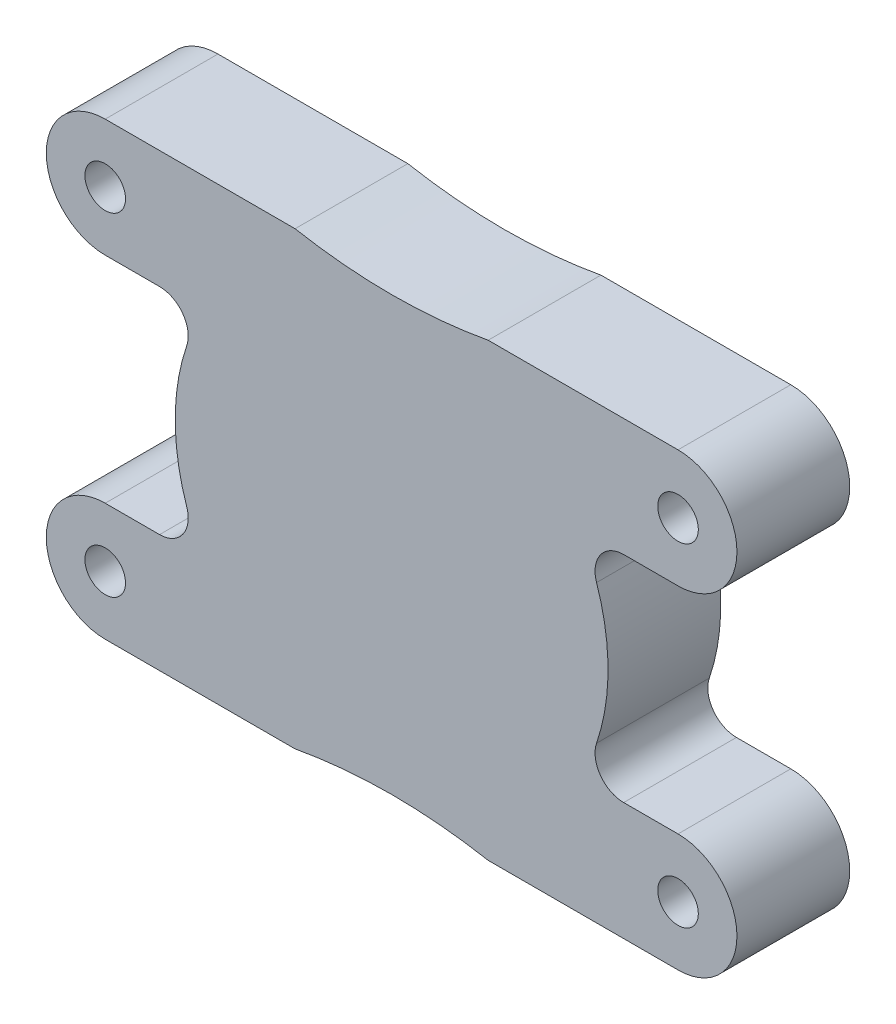
SolidWorks part; units mm, degrees
ref_plane "Front Plane" through (0, 0, 0) normal (0, 0, 1) x (1, 0, 0)
ref_plane "Top Plane" through (0, 0, 0) normal (0, 1, 0) x (1, 0, 0)
ref_plane "Right Plane" through (0, 0, 0) normal (1, 0, 0) x (0, 0, -1)
sketch "Sketch1" plane through (0, 0, 0) normal (0, 0, 1) x (1, 0, 0)
  line L8 (8.5626, -19.975) -> (25.4, -19.975)
  line L9 (25.4, -9.525) -> (20.5798, -9.525)
  line L10 (20.5798, 9.525) -> (25.4, 9.525)
  line L11 (25.4, 19.975) -> (8.5626, 19.975)
  line L12 (-8.5626, 19.975) -> (-25.4, 19.975)
  line L13 (-25.4, 9.525) -> (-20.5798, 9.525)
  line L14 (-20.5798, -9.525) -> (-25.4, -9.525)
  line L15 (-25.4, -19.975) -> (-8.5626, -19.975)
  line L16 (8.5626, -19.975) -> (25.4, -19.975)
  line L17 (25.4, -9.525) -> (20.5798, -9.525)
  line L18 (20.5798, 9.525) -> (25.4, 9.525)
  line L19 (25.4, 19.975) -> (8.5626, 19.975)
  line L20 (-8.5626, 19.975) -> (-25.4, 19.975)
  line L21 (-25.4, 9.525) -> (-20.5798, 9.525)
  line L22 (-20.5798, -9.525) -> (-25.4, -9.525)
  line L23 (-25.4, -19.975) -> (-8.5626, -19.975)
  circle A0 centre (-25.4, -14.75) radius 1.8 construction
  circle A1 centre (-25.4, 14.75) radius 1.8 construction
  circle A2 centre (25.4, -14.75) radius 1.8 construction
  circle A3 centre (25.4, 14.75) radius 1.8 construction
  circle A4 centre (-25.4, 14.75) radius 1.8
  circle A5 centre (-25.4, -14.75) radius 1.8
  circle A6 centre (25.4, -14.75) radius 1.8
  circle A7 centre (25.4, 14.75) radius 1.8
  arc A12 (8.5626, -19.975) -> (-8.5626, -19.975) centre (0, -66.4554) ccw
  arc A13 (25.4, -19.975) -> (25.4, -9.525) centre (25.4, -14.75) ccw
  arc A14 (18.1746, -6.1686) -> (20.5798, -9.525) centre (20.5798, -6.985) ccw
  arc A15 (18.1746, -6.1686) -> (18.1746, 6.1686) centre (0, 0) ccw
  arc A16 (20.5798, 9.525) -> (18.1746, 6.1686) centre (20.5798, 6.985) ccw
  arc A17 (25.4, 9.525) -> (25.4, 19.975) centre (25.4, 14.75) ccw
  arc A18 (-8.5626, 19.975) -> (8.5626, 19.975) centre (0, 66.4554) ccw
  arc A19 (-25.4, 19.975) -> (-25.4, 9.525) centre (-25.4, 14.75) ccw
  arc A20 (-18.1746, 6.1686) -> (-20.5798, 9.525) centre (-20.5798, 6.985) ccw
  arc A21 (-18.1746, 6.1686) -> (-18.1746, -6.1686) centre (0, 0) ccw
  arc A22 (-20.5798, -9.525) -> (-18.1746, -6.1686) centre (-20.5798, -6.985) ccw
  arc A23 (-25.4, -9.525) -> (-25.4, -19.975) centre (-25.4, -14.75) ccw
  arc A24 (8.5626, -19.975) -> (-8.5626, -19.975) centre (0, -66.4554) ccw
  arc A25 (25.4, -19.975) -> (25.4, -9.525) centre (25.4, -14.75) ccw
  arc A26 (18.1746, -6.1686) -> (20.5798, -9.525) centre (20.5798, -6.985) ccw
  arc A27 (18.1746, -6.1686) -> (18.1746, 6.1686) centre (0, 0) ccw
  arc A28 (20.5798, 9.525) -> (18.1746, 6.1686) centre (20.5798, 6.985) ccw
  arc A29 (25.4, 9.525) -> (25.4, 19.975) centre (25.4, 14.75) ccw
  arc A30 (-8.5626, 19.975) -> (8.5626, 19.975) centre (0, 66.4554) ccw
  arc A31 (-25.4, 19.975) -> (-25.4, 9.525) centre (-25.4, 14.75) ccw
  arc A32 (-18.1746, 6.1686) -> (-20.5798, 9.525) centre (-20.5798, 6.985) ccw
  arc A33 (-18.1746, 6.1686) -> (-18.1746, -6.1686) centre (0, 0) ccw
  arc A34 (-20.5798, -9.525) -> (-18.1746, -6.1686) centre (-20.5798, -6.985) ccw
  arc A35 (-25.4, -9.525) -> (-25.4, -19.975) centre (-25.4, -14.75) ccw
  dimension "D1" = 0
extrude "Boss-Extrude1" add sketch "Sketch1" along normal blind 10
